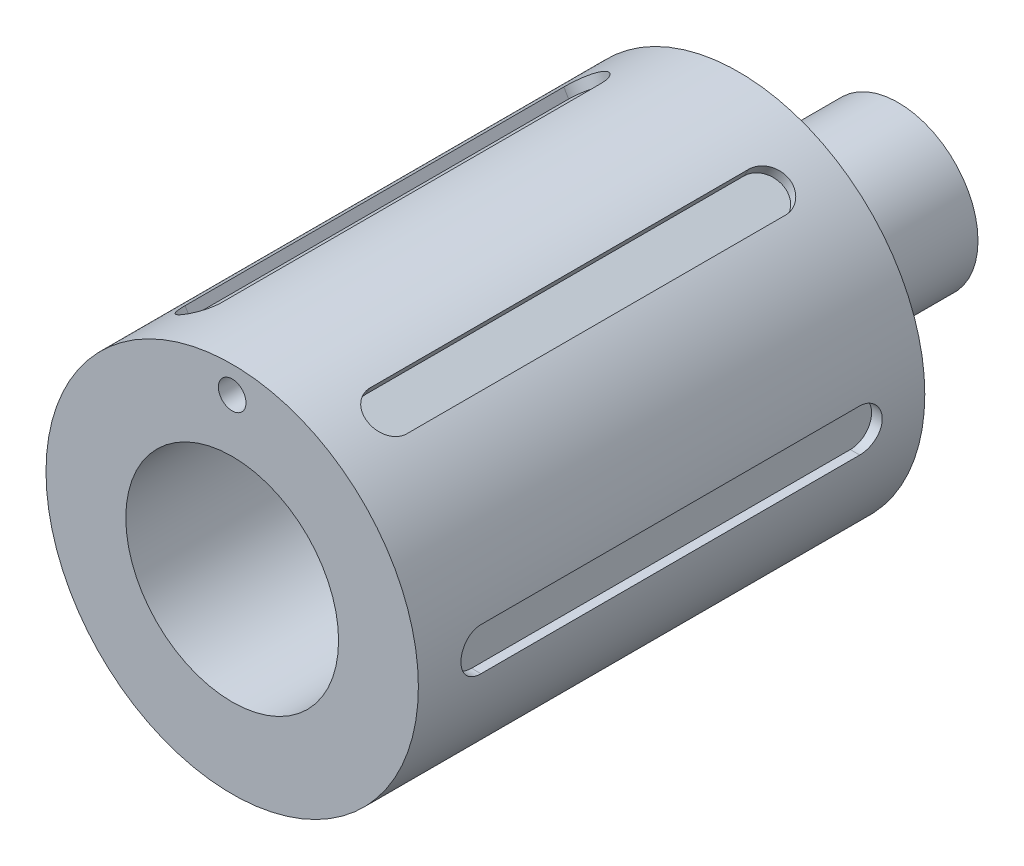
SolidWorks part; units mm, degrees
material "Plain Carbon Steel"
ref_plane "Front" through (0, 0, 0) normal (0, 0, 1) x (1, 0, 0)
ref_plane "Top" through (0, 0, 0) normal (0, 1, 0) x (1, 0, 0)
ref_plane "Right" through (0, 0, 0) normal (1, 0, 0) x (0, 0, -1)
sketch "Sketch1" plane through (0, 0, 0) normal (1, 0, 0) x (0, 0, -1)
  line L0 (0, 0) -> (79.502, 0) construction
  line L1 (0, 12.7) -> (0, 22.225)
  line L2 (0, 22.225) -> (60.452, 22.225)
  line L3 (60.452, 22.225) -> (60.452, 9.525)
  line L4 (60.452, 9.525) -> (79.502, 9.525)
  line L5 (79.502, 9.525) -> (79.502, 0)
  line L6 (79.502, 0) -> (57.15, 0)
  line L7 (57.15, 0) -> (57.15, 12.7)
  line L8 (57.15, 12.7) -> (0, 12.7)
  dimension "D1" = 79.502
  dimension "D2" = 19.05
  dimension "D3" = 44.45
  dimension "D4" = 25.4
  dimension "D5" = 57.15
  dimension "D6" = 19.05
revolve "Revolve1" add sketch "Sketch1" angle 360 about L0
ref_plane "Plane1" through (22.225, 0, 0) normal (1, 0, 0) x (0, 0, -1)
sketch "Sketch2" plane through (22.225, 0, 0) normal (1, 0, 0) x (0, 0, -1)
  line L0 (7.62, 0) -> (52.832, 0) construction
  line L1 (7.62, 2.54) -> (52.832, 2.54)
  line L2 (7.62, -2.54) -> (52.832, -2.54)
  line L3 (0, 22.225) -> (0, -22.225) construction
  arc A0 (7.62, 2.54) -> (7.62, -2.54) centre (7.62, 0) ccw
  arc A1 (52.832, -2.54) -> (52.832, 2.54) centre (52.832, 0) ccw
  point P3 (30.226, 0)
  dimension "D1" = 2.54
  dimension "D2" = 45.212
  dimension "D3" = 7.62
extrude "Cut-Extrude1" cut sketch "Sketch2" against normal blind 1.27
pattern_circular "CirPattern1" count 6 over 360 about axis through (0, 0, 0) along (0, 0, 1) of "Cut-Extrude1"
hole_wizard "3/4 (0.13) Diameter Hole1" positions "Sketch3" profile "Sketch4" hole size "3/4" standard "ANSI Inch"
sketch "Sketch3" plane through (0, 0, 0) normal (0, 0, 1) x (1, 0, 0)
  point P0 (0, 19.05)
  point P4 (0, 0)
  dimension "D1" = 19.05
sketch "Sketch4" plane through (0, 19.05, 0) normal (1, 0, 0) x (0, -1, 0)
  line L0 (0, 0) -> (0, 16.867)
  line L1 (0, 16.867) -> (1.651, 15.875)
  line L2 (1.651, 15.875) -> (1.651, 0)
  line L5 (1.651, 0) -> (0, 0)
  line L10 (0, 16.867) -> (-1.651, 15.875) construction
  line L11 (0, -6.35) -> (0, 107.95) construction
  dimension "Hole Dia." = 3.302
  dimension "Hole Depth" = 15.875
  dimension "Drill Angle" = 118
